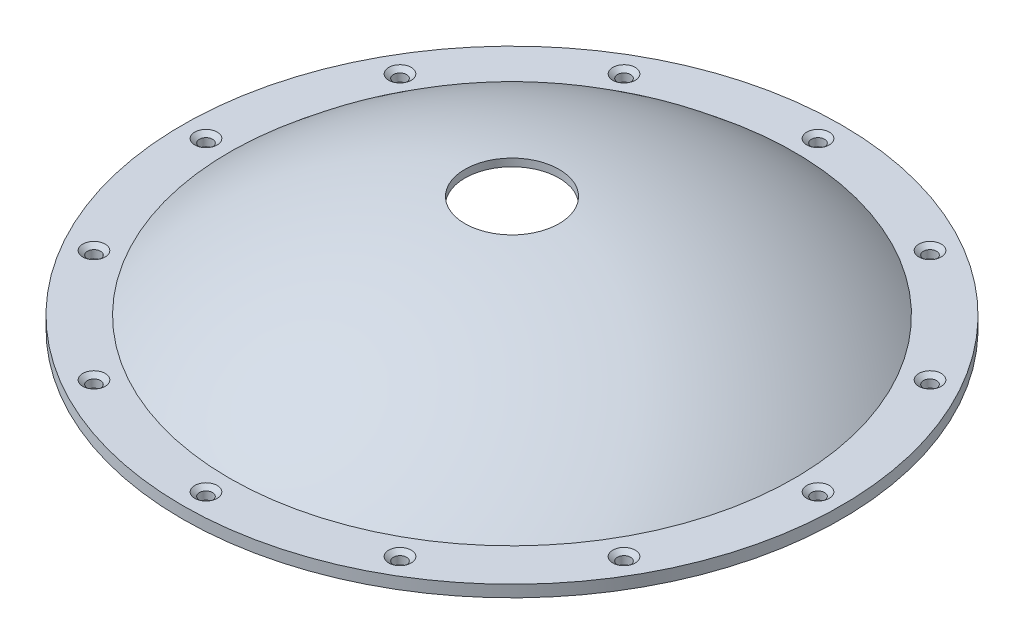
SolidWorks part; units mm, degrees
material "6063-T6"
ref_plane "Front Plane" through (0, 0, 0) normal (0, 0, 1) x (1, 0, 0)
ref_plane "Top Plane" through (0, 0, 0) normal (0, 1, 0) x (1, 0, 0)
ref_plane "Right Plane" through (0, 0, 0) normal (1, 0, 0) x (0, 0, -1)
ref_axis "Axis1" through (0, 55, 0) along (0, -1, 0)
sketch "Sketch1" plane through (0, 0, 0) normal (0, 0, 1) x (1, 0, 0)
  line L0 (-44.45, 0) -> (-38.1, 0)
  line L1 (0, 55) -> (0, -55) construction
  line L2 (-44.45, 0) -> (-44.45, 1.5875)
  line L3 (-44.45, 1.5875) -> (-38.1, 1.5875)
  line L4 (-38.1, 0) -> (-38.1, -4.7625) construction
  line L5 (-6.35, 15.455) -> (-6.35, 14.4328)
  line L6 (-38.1, 0) -> (0, 0) construction
  line L8 (-6.35, 15.455) -> (-6.35, 14.4328) construction
  arc A0 (-37.9246, 0.39) -> (-38.1, 0) centre (-37.5787, 0) ccw
  arc A1 (-37.9246, 0.39) -> (-6.35, 14.4328) centre (0, -42.3633) cw
  arc A2 (-38.1, 1.5875) -> (-6.35, 15.455) centre (0, -42.3633) cw
  point P13 (-7.8019, 14.2516)
  dimension "D3" = 57.15
  dimension "D5" = 1.016
revolve "Revolve1" add sketch "Sketch1" angle 360 about axis through (0, 55, 0) along (0, -1, 0)
ref_plane "Hole Location Plane" through (0, 3.175, 0) normal (0, 1, 0) x (1, 0, 0)
sketch "Hole Location" plane through (0, 3.175, 0) normal (0, 1, 0) x (1, 0, 0)
  line L0 (0, 0) -> (-41.275, 0) construction
  circle A0 centre (0, 0) radius 41.275 construction
  dimension "D1" = 82.55
hole_wizard "CSK for #0 Flat Head Machine Screw (100)1" positions "Sketch4" profile "Sketch5" countersink size "#0" standard "ANSI Inch" end condition through all
sketch "Sketch4" plane through (0, 1.5875, 0) normal (0, 1, 0) x (1, 0, 0)
  point P0 (-41.275, 0)
sketch "Sketch5" plane through (-41.275, 1.5875, 0) normal (1, 0, 0) x (0, 0, 1)
  line L0 (0, 0) -> (0, 1.5875)
  line L1 (0, 1.5875) -> (0.889, 1.5875)
  line L2 (0.889, 1.5875) -> (0.889, 0.5222)
  line L3 (0.889, 0.5222) -> (1.5113, 0)
  line L5 (1.5113, 0) -> (0, 0)
  line L6 (-0.889, 0.5222) -> (-1.5113, 0) construction
  line L11 (0, -6.35) -> (0, 107.95) construction
  dimension "Thru Hole Dia." = 1.778
  dimension "Thru Hole Depth" = 1.5875
  dimension "Near C'Sink Dia." = 3.0226
  dimension "Near C'Sink Angle" = 100
pattern_circular "CirPattern1" count 12 every 30 about axis through (0, 0, 0) along (0, 1, 0) of "CSK for #0 Flat Head Machine Screw (100)1"
equation "\"D3@Sketch1\"=\"TANK DIAMETER@Cryo Tank.Assembly\"*0.75"
equation "\"D1@Hole Location\"=\"TANK DIAMETER@Cryo Tank.Assembly\"+\"GASKET SEAT THICKNESS@Cryo Tank.Assembly\""
